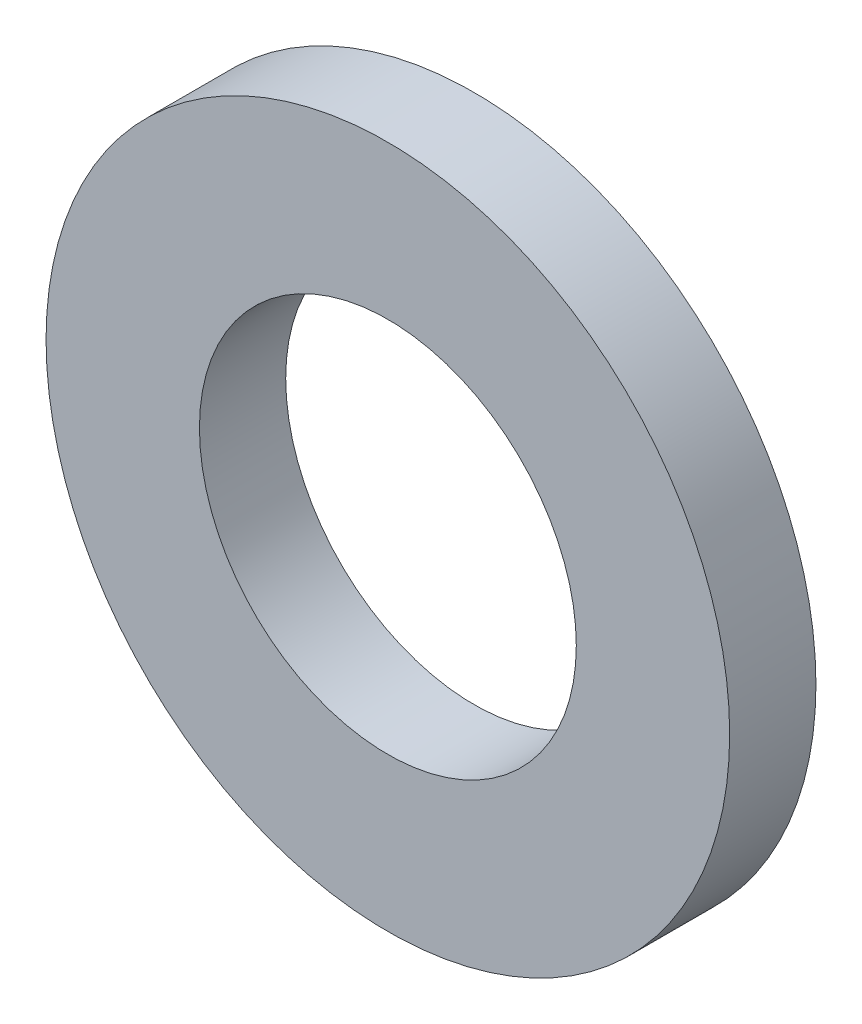
SolidWorks part; units mm, degrees
ref_plane "Front Plane" through (0, 0, 0) normal (0, 0, 1) x (1, 0, 0)
ref_plane "Top Plane" through (0, 0, 0) normal (0, 1, 0) x (1, 0, 0)
ref_plane "Right Plane" through (0, 0, 0) normal (1, 0, 0) x (0, 0, -1)
sketch "Sketch1" plane through (0, 0, 0) normal (0, 0, 1) x (1, 0, 0)
  circle A0 centre (0, 0) radius 2.1844
  circle A1 centre (0, 0) radius 3.9624
  dimension "ID" = 4.3688
  dimension "OD" = 7.9248
extrude "Extrude1" add sketch "Sketch1" against normal blind 1
